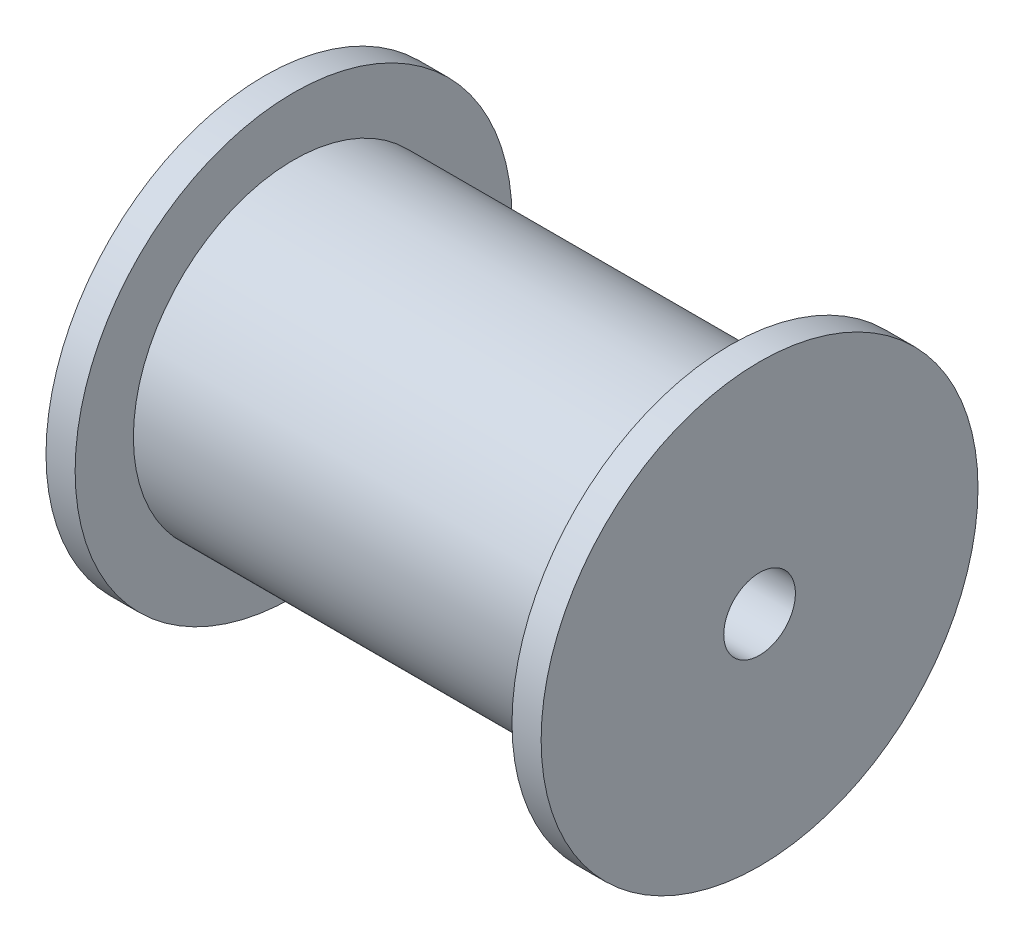
SolidWorks part; units mm, degrees
ref_plane "Front Plane" through (0, 0, 0) normal (0, 0, 1) x (1, 0, 0)
ref_plane "Top Plane" through (0, 0, 0) normal (0, 1, 0) x (1, 0, 0)
ref_plane "Right Plane" through (0, 0, 0) normal (1, 0, 0) x (0, 0, -1)
sketch "Sketch1" plane through (0, 0, 0) normal (0, 0, 1) x (1, 0, 0)
  line L0 (-25.4, 0) -> (25.4, 0)
  line L1 (25.4, 0) -> (25.4, 19.05)
  line L2 (25.4, 19.05) -> (22.86, 19.05)
  line L3 (22.86, 19.05) -> (22.86, 13.97)
  line L4 (22.86, 13.97) -> (-15.24, 13.97)
  line L5 (-15.24, 13.97) -> (-15.24, 19.05)
  line L6 (-15.24, 19.05) -> (-17.78, 19.05)
  line L7 (-17.78, 19.05) -> (-17.78, 6.35)
  line L8 (-17.78, 6.35) -> (-25.4, 6.35)
  line L9 (-25.4, 6.35) -> (-25.4, 0)
  dimension "D1" = 50.8
  dimension "D2" = 19.05
  dimension "D3" = 2.54
  dimension "D4" = 2.54
  dimension "D5" = 5.08
  dimension "D6" = 6.35
  dimension "D7" = 7.62
revolve "Revolve1" add sketch "Sketch1" angle 360 about L0
sketch "Sketch2" plane through (-25.4, 0, 0) normal (-1, 0, 0) x (0, 0, 1)
  circle A0 centre (0, 0) radius 3.1242
  dimension "D1" = 6.2484
extrude "Cut-Extrude1" cut sketch "Sketch2" against normal through all
ref_plane "Mid-Plane" through (3.81, 0, 0) normal (1, 0, 0) x (0, 0, -1)
